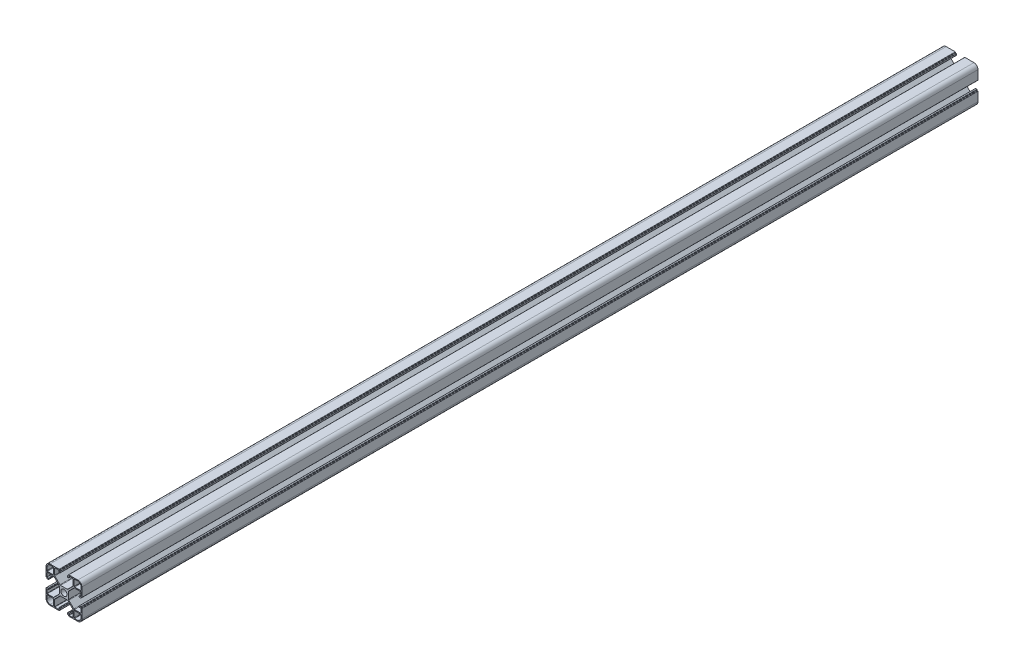
SolidWorks part; units mm, degrees
material "6063 T5"
ref_plane "Спереди" through (0, 0, 0) normal (0, 0, 1) x (1, 0, 0)
ref_plane "Сверху" through (0, 0, 0) normal (0, 1, 0) x (1, 0, 0)
ref_plane "Справа" through (0, 0, 0) normal (1, 0, 0) x (0, 0, -1)
sketch "Эскиз1" plane through (0, 0, 0) normal (0, 0, 1) x (1, 0, 0)
  line L0 (-19.98, 20.5457) -> (20.02, 20.5457) construction
  line L1 (-20, 10.4) -> (-20, 15.5)
  line L2 (-15.5, 20) -> (-10.4, 20)
  line L3 (10.4, 20) -> (15.5, 20)
  line L4 (-11.9, 11.4) -> (-18.5, 11.4)
  line L5 (-11.4, 11.9) -> (-11.4, 18.5)
  line L6 (-11.9, 19) -> (-15.5, 19)
  line L7 (-19, 11.9) -> (-19, 15.5)
  line L8 (20, 15.5) -> (20, 10.4)
  line L9 (11.4, 11.9) -> (11.4, 18.5)
  line L10 (11.9, 11.4) -> (18.5, 11.4)
  line L11 (19, 11.9) -> (19, 15.5)
  line L12 (11.9, 19) -> (15.5, 19)
  line L13 (20, -10.4) -> (20, -15.5)
  line L14 (15.5, -20) -> (10.4, -20)
  line L15 (11.9, -11.4) -> (18.5, -11.4)
  line L16 (11.4, -11.9) -> (11.4, -18.5)
  line L17 (11.9, -19) -> (15.5, -19)
  line L18 (19, -11.9) -> (19, -15.5)
  line L19 (-10.4, -20) -> (-15.5, -20)
  line L20 (-20, -15.5) -> (-20, -10.4)
  line L21 (-11.4, -11.9) -> (-11.4, -18.5)
  line L22 (-11.9, -11.4) -> (-18.5, -11.4)
  line L23 (-19, -11.9) -> (-19, -15.5)
  line L24 (-11.9, -19) -> (-15.5, -19)
  line L25 (0, 0) -> (-11.4, 11.9) construction
  line L26 (-20.0149, 25.4879) -> (19.9851, 25.4879) construction
  arc A0 (-20, 15.5) -> (-15.5, 20) centre (-15.5, 15.5) cw
  arc A1 (-15.5, 19) -> (-19, 15.5) centre (-15.5, 15.5) ccw
  arc A2 (-18.5, 11.4) -> (-19, 11.9) centre (-18.5, 11.9) cw
  arc A3 (-11.9, 11.4) -> (-11.4, 11.9) centre (-11.9, 11.9) ccw
  arc A4 (-11.4, 18.5) -> (-11.9, 19) centre (-11.9, 18.5) ccw
  circle A5 centre (0, 0) radius 3.4
  arc A6 (15.5, 20) -> (20, 15.5) centre (15.5, 15.5) cw
  arc A7 (19, 15.5) -> (15.5, 19) centre (15.5, 15.5) ccw
  arc A8 (11.4, 18.5) -> (11.9, 19) centre (11.9, 18.5) cw
  arc A9 (11.4, 11.9) -> (11.9, 11.4) centre (11.9, 11.9) ccw
  arc A10 (18.5, 11.4) -> (19, 11.9) centre (18.5, 11.9) ccw
  arc A11 (20, -15.5) -> (15.5, -20) centre (15.5, -15.5) cw
  arc A12 (15.5, -19) -> (19, -15.5) centre (15.5, -15.5) ccw
  arc A13 (18.5, -11.4) -> (19, -11.9) centre (18.5, -11.9) cw
  arc A14 (11.9, -11.4) -> (11.4, -11.9) centre (11.9, -11.9) ccw
  arc A15 (11.4, -18.5) -> (11.9, -19) centre (11.9, -18.5) ccw
  arc A16 (-15.5, -20) -> (-20, -15.5) centre (-15.5, -15.5) cw
  arc A17 (-19, -15.5) -> (-15.5, -19) centre (-15.5, -15.5) ccw
  arc A18 (-11.4, -18.5) -> (-11.9, -19) centre (-11.9, -18.5) cw
  arc A19 (-11.4, -11.9) -> (-11.9, -11.4) centre (-11.9, -11.9) ccw
  arc A20 (-18.5, -11.4) -> (-19, -11.9) centre (-18.5, -11.9) ccw
  point P5 (0, 0)
  line B0 (-20, 10.4) -> (-20, 5.4)
  line B1 (-19.7, 5.1) -> (-19.3, 5.1)
  line B2 (-19, 4.8) -> (-19, 4.4)
  line B3 (-18.7, 4.1) -> (-17.3, 4.1)
  line B4 (-17, 4.4) -> (-17, 5.3)
  line B5 (-17.3, 5.6) -> (-18.7, 5.6)
  line B6 (-19, 5.9) -> (-19, 10.1)
  line B7 (-18.7, 10.4) -> (-11.8142, 10.4)
  line B8 (-11.1071, 10.1071) -> (-5.4929, 4.4929)
  line B9 (-5.2, 3.7858) -> (-5.2, -3.7858)
  line B10 (-5.2, 0) -> (-20, 0) construction
  line B11 (-11.1071, -10.1071) -> (-5.4929, -4.4929)
  line B12 (-18.7, -10.4) -> (-11.8142, -10.4)
  line B13 (-19, -5.9) -> (-19, -10.1)
  line B14 (-17.3, -5.6) -> (-18.7, -5.6)
  line B15 (-17, -4.4) -> (-17, -5.3)
  line B16 (-18.7, -4.1) -> (-17.3, -4.1)
  line B17 (-19, -4.8) -> (-19, -4.4)
  line B18 (-19.7, -5.1) -> (-19.3, -5.1)
  line B19 (-20, -10.4) -> (-20, -5.4)
  arc B20 (-17, 5.3) -> (-17.3, 5.6) centre (-17.3, 5.3) ccw
  arc B21 (-17.3, 4.1) -> (-17, 4.4) centre (-17.3, 4.4) ccw
  arc B22 (-19, 4.4) -> (-18.7, 4.1) centre (-18.7, 4.4) ccw
  arc B23 (-19.3, 5.1) -> (-19, 4.8) centre (-19.3, 4.8) cw
  arc B24 (-20, 5.4) -> (-19.7, 5.1) centre (-19.7, 5.4) ccw
  arc B25 (-5.4929, 4.4929) -> (-5.2, 3.7858) centre (-6.2, 3.7858) cw
  arc B26 (-11.8142, 10.4) -> (-11.1071, 10.1071) centre (-11.8142, 9.4) cw
  arc B27 (-19, 10.1) -> (-18.7, 10.4) centre (-18.7, 10.1) cw
  arc B28 (-18.7, 5.6) -> (-19, 5.9) centre (-18.7, 5.9) cw
  arc B29 (-18.7, -5.6) -> (-19, -5.9) centre (-18.7, -5.9) ccw
  arc B30 (-19, -10.1) -> (-18.7, -10.4) centre (-18.7, -10.1) ccw
  arc B31 (-11.8142, -10.4) -> (-11.1071, -10.1071) centre (-11.8142, -9.4) ccw
  arc B32 (-5.4929, -4.4929) -> (-5.2, -3.7858) centre (-6.2, -3.7858) ccw
  arc B33 (-20, -5.4) -> (-19.7, -5.1) centre (-19.7, -5.4) cw
  arc B34 (-19.3, -5.1) -> (-19, -4.8) centre (-19.3, -4.8) ccw
  arc B35 (-19, -4.4) -> (-18.7, -4.1) centre (-18.7, -4.4) cw
  arc B36 (-17.3, -4.1) -> (-17, -4.4) centre (-17.3, -4.4) cw
  arc B37 (-17, -5.3) -> (-17.3, -5.6) centre (-17.3, -5.3) cw
  line B38 (10.4, 20) -> (5.4, 20)
  line B39 (5.1, 19.7) -> (5.1, 19.3)
  line B40 (4.8, 19) -> (4.4, 19)
  line B41 (4.1, 18.7) -> (4.1, 17.3)
  line B42 (4.4, 17) -> (5.3, 17)
  line B43 (5.6, 17.3) -> (5.6, 18.7)
  line B44 (5.9, 19) -> (10.1, 19)
  line B45 (10.4, 18.7) -> (10.4, 11.8142)
  line B46 (10.1071, 11.1071) -> (4.4929, 5.4929)
  line B47 (3.7858, 5.2) -> (-3.7858, 5.2)
  line B48 (0, 5.2) -> (0, 20) construction
  line B49 (-10.1071, 11.1071) -> (-4.4929, 5.4929)
  line B50 (-10.4, 18.7) -> (-10.4, 11.8142)
  line B51 (-5.9, 19) -> (-10.1, 19)
  line B52 (-5.6, 17.3) -> (-5.6, 18.7)
  line B53 (-4.4, 17) -> (-5.3, 17)
  line B54 (-4.1, 18.7) -> (-4.1, 17.3)
  line B55 (-4.8, 19) -> (-4.4, 19)
  line B56 (-5.1, 19.7) -> (-5.1, 19.3)
  line B57 (-10.4, 20) -> (-5.4, 20)
  arc B58 (5.3, 17) -> (5.6, 17.3) centre (5.3, 17.3) ccw
  arc B59 (4.1, 17.3) -> (4.4, 17) centre (4.4, 17.3) ccw
  arc B60 (4.4, 19) -> (4.1, 18.7) centre (4.4, 18.7) ccw
  arc B61 (5.1, 19.3) -> (4.8, 19) centre (4.8, 19.3) cw
  arc B62 (5.4, 20) -> (5.1, 19.7) centre (5.4, 19.7) ccw
  arc B63 (4.4929, 5.4929) -> (3.7858, 5.2) centre (3.7858, 6.2) cw
  arc B64 (10.4, 11.8142) -> (10.1071, 11.1071) centre (9.4, 11.8142) cw
  arc B65 (10.1, 19) -> (10.4, 18.7) centre (10.1, 18.7) cw
  arc B66 (5.6, 18.7) -> (5.9, 19) centre (5.9, 18.7) cw
  arc B67 (-5.6, 18.7) -> (-5.9, 19) centre (-5.9, 18.7) ccw
  arc B68 (-10.1, 19) -> (-10.4, 18.7) centre (-10.1, 18.7) ccw
  arc B69 (-10.4, 11.8142) -> (-10.1071, 11.1071) centre (-9.4, 11.8142) ccw
  arc B70 (-4.4929, 5.4929) -> (-3.7858, 5.2) centre (-3.7858, 6.2) ccw
  arc B71 (-5.4, 20) -> (-5.1, 19.7) centre (-5.4, 19.7) cw
  arc B72 (-5.1, 19.3) -> (-4.8, 19) centre (-4.8, 19.3) ccw
  arc B73 (-4.4, 19) -> (-4.1, 18.7) centre (-4.4, 18.7) cw
  arc B74 (-4.1, 17.3) -> (-4.4, 17) centre (-4.4, 17.3) cw
  arc B75 (-5.3, 17) -> (-5.6, 17.3) centre (-5.3, 17.3) cw
  line B76 (20, -10.4) -> (20, -5.4)
  line B77 (19.7, -5.1) -> (19.3, -5.1)
  line B78 (19, -4.8) -> (19, -4.4)
  line B79 (18.7, -4.1) -> (17.3, -4.1)
  line B80 (17, -4.4) -> (17, -5.3)
  line B81 (17.3, -5.6) -> (18.7, -5.6)
  line B82 (19, -5.9) -> (19, -10.1)
  line B83 (18.7, -10.4) -> (11.8142, -10.4)
  line B84 (11.1071, -10.1071) -> (5.4929, -4.4929)
  line B85 (5.2, -3.7858) -> (5.2, 3.7858)
  line B86 (5.2, 0) -> (20, 0) construction
  line B87 (11.1071, 10.1071) -> (5.4929, 4.4929)
  line B88 (18.7, 10.4) -> (11.8142, 10.4)
  line B89 (19, 5.9) -> (19, 10.1)
  line B90 (17.3, 5.6) -> (18.7, 5.6)
  line B91 (17, 4.4) -> (17, 5.3)
  line B92 (18.7, 4.1) -> (17.3, 4.1)
  line B93 (19, 4.8) -> (19, 4.4)
  line B94 (19.7, 5.1) -> (19.3, 5.1)
  line B95 (20, 10.4) -> (20, 5.4)
  arc B96 (17, -5.3) -> (17.3, -5.6) centre (17.3, -5.3) ccw
  arc B97 (17.3, -4.1) -> (17, -4.4) centre (17.3, -4.4) ccw
  arc B98 (19, -4.4) -> (18.7, -4.1) centre (18.7, -4.4) ccw
  arc B99 (19.3, -5.1) -> (19, -4.8) centre (19.3, -4.8) cw
  arc B100 (20, -5.4) -> (19.7, -5.1) centre (19.7, -5.4) ccw
  arc B101 (5.4929, -4.4929) -> (5.2, -3.7858) centre (6.2, -3.7858) cw
  arc B102 (11.8142, -10.4) -> (11.1071, -10.1071) centre (11.8142, -9.4) cw
  arc B103 (19, -10.1) -> (18.7, -10.4) centre (18.7, -10.1) cw
  arc B104 (18.7, -5.6) -> (19, -5.9) centre (18.7, -5.9) cw
  arc B105 (18.7, 5.6) -> (19, 5.9) centre (18.7, 5.9) ccw
  arc B106 (19, 10.1) -> (18.7, 10.4) centre (18.7, 10.1) ccw
  arc B107 (11.8142, 10.4) -> (11.1071, 10.1071) centre (11.8142, 9.4) ccw
  arc B108 (5.4929, 4.4929) -> (5.2, 3.7858) centre (6.2, 3.7858) ccw
  arc B109 (20, 5.4) -> (19.7, 5.1) centre (19.7, 5.4) cw
  arc B110 (19.3, 5.1) -> (19, 4.8) centre (19.3, 4.8) ccw
  arc B111 (19, 4.4) -> (18.7, 4.1) centre (18.7, 4.4) cw
  arc B112 (17.3, 4.1) -> (17, 4.4) centre (17.3, 4.4) cw
  arc B113 (17, 5.3) -> (17.3, 5.6) centre (17.3, 5.3) cw
  line B114 (-10.4, -20) -> (-5.4, -20)
  line B115 (-5.1, -19.7) -> (-5.1, -19.3)
  line B116 (-4.8, -19) -> (-4.4, -19)
  line B117 (-4.1, -18.7) -> (-4.1, -17.3)
  line B118 (-4.4, -17) -> (-5.3, -17)
  line B119 (-5.6, -17.3) -> (-5.6, -18.7)
  line B120 (-5.9, -19) -> (-10.1, -19)
  line B121 (-10.4, -18.7) -> (-10.4, -11.8142)
  line B122 (-10.1071, -11.1071) -> (-4.4929, -5.4929)
  line B123 (-3.7858, -5.2) -> (3.7858, -5.2)
  line B124 (0, -5.2) -> (0, -20) construction
  line B125 (10.1071, -11.1071) -> (4.4929, -5.4929)
  line B126 (10.4, -18.7) -> (10.4, -11.8142)
  line B127 (5.9, -19) -> (10.1, -19)
  line B128 (5.6, -17.3) -> (5.6, -18.7)
  line B129 (4.4, -17) -> (5.3, -17)
  line B130 (4.1, -18.7) -> (4.1, -17.3)
  line B131 (4.8, -19) -> (4.4, -19)
  line B132 (5.1, -19.7) -> (5.1, -19.3)
  line B133 (10.4, -20) -> (5.4, -20)
  arc B134 (-5.3, -17) -> (-5.6, -17.3) centre (-5.3, -17.3) ccw
  arc B135 (-4.1, -17.3) -> (-4.4, -17) centre (-4.4, -17.3) ccw
  arc B136 (-4.4, -19) -> (-4.1, -18.7) centre (-4.4, -18.7) ccw
  arc B137 (-5.1, -19.3) -> (-4.8, -19) centre (-4.8, -19.3) cw
  arc B138 (-5.4, -20) -> (-5.1, -19.7) centre (-5.4, -19.7) ccw
  arc B139 (-4.4929, -5.4929) -> (-3.7858, -5.2) centre (-3.7858, -6.2) cw
  arc B140 (-10.4, -11.8142) -> (-10.1071, -11.1071) centre (-9.4, -11.8142) cw
  arc B141 (-10.1, -19) -> (-10.4, -18.7) centre (-10.1, -18.7) cw
  arc B142 (-5.6, -18.7) -> (-5.9, -19) centre (-5.9, -18.7) cw
  arc B143 (5.6, -18.7) -> (5.9, -19) centre (5.9, -18.7) ccw
  arc B144 (10.1, -19) -> (10.4, -18.7) centre (10.1, -18.7) ccw
  arc B145 (10.4, -11.8142) -> (10.1071, -11.1071) centre (9.4, -11.8142) ccw
  arc B146 (4.4929, -5.4929) -> (3.7858, -5.2) centre (3.7858, -6.2) ccw
  arc B147 (5.4, -20) -> (5.1, -19.7) centre (5.4, -19.7) cw
  arc B148 (5.1, -19.3) -> (4.8, -19) centre (4.8, -19.3) ccw
  arc B149 (4.4, -19) -> (4.1, -18.7) centre (4.4, -18.7) cw
  arc B150 (4.1, -17.3) -> (4.4, -17) centre (4.4, -17.3) cw
  arc B151 (5.3, -17) -> (5.6, -17.3) centre (5.3, -17.3) cw
  dimension "D2" = 4.5
  dimension "D3" = 3.5
  dimension "D5" = 0.5
  dimension "D6" = 6.8
  dimension "D1" = 20
  dimension "D4" = 7.6
  dimension "D7" = 40
sketch_block_instance "8B(20,5PL)-1"
sketch_block "8B(20,5PL)" parameters "D7"=0.3, "D8"=1, "D13"=1, "D1"=14.8, "D2"=3, "D3"=8.2, "D4"=20.8, "D5"=10.2, "D6"=135, "D9"=4.85, "D10"=1.2, "D11"=2.15, "D12"=11.8
sketch_block_instance "8B(20,5PL)-3"
sketch_block_instance "8B(20,5PL)-4"
sketch_block_instance "8B(20,5PL)-5"
extrude "Бобышка-Вытянуть1" add sketch "Эскиз1" along normal blind 1000 contours B151 B129 B150 B130 B149 B131 B148 B132 B147 B133 L14 A11 L13 B76 B100 B77 B99 B78 B98 B79 B97 B80 B96 B81 B104 B82 B103 B83 B102 B84 B101 B85 B108 B87 B107 B88 B106 B89 B105 B90 B113 B91 B112 B92 B111 B93 B110 B94 B109 B95 L8
